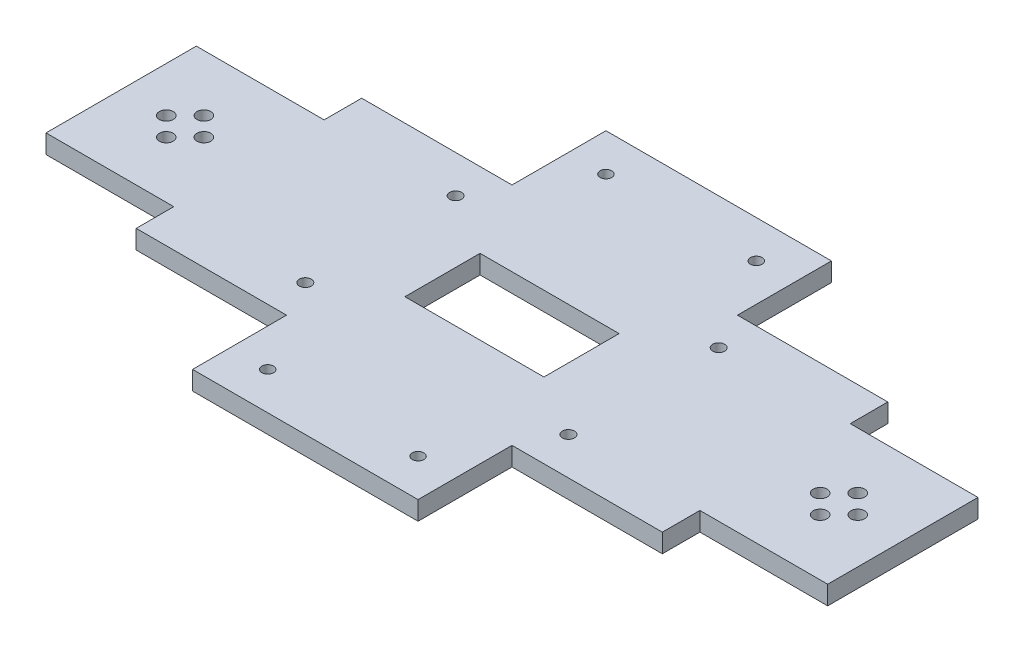
SolidWorks part; units mm, degrees
ref_plane "Front Plane" through (0, 0, 0) normal (0, 0, 1) x (1, 0, 0)
ref_plane "Top Plane" through (0, 0, 0) normal (0, 1, 0) x (1, 0, 0)
ref_plane "Right Plane" through (0, 0, 0) normal (1, 0, 0) x (0, 0, -1)
sketch "Sketch1" plane through (0, 0, 0) normal (0, 1, 0) x (1, 0, 0)
  line L0 (0, 50) -> (0, -43.3333) construction
  line L1 (104, 0) -> (87, 0) construction
  line L2 (-70, 30) -> (70, 30)
  line L3 (0, 30) -> (0, -30)
  line L4 (-70, -30) -> (70, -30)
  line L5 (70, 30) -> (70, -30)
  line L6 (70, 20) -> (104, 20)
  line L7 (70, 20) -> (70, -20)
  line L8 (70, -20) -> (104, -20)
  line L9 (104, 20) -> (104, -20)
  line L10 (104, 20) -> (70, 20) construction
  line L11 (87, 0) -> (104, 0) construction
  line L13 (104, 0) -> (87, 0) construction
  line L14 (87, 0) -> (87, 15) construction
  line L15 (-87, 0) -> (-87, 15) construction
  line L16 (-104, 0) -> (-87, 0) construction
  line L17 (-87, 0) -> (-104, 0) construction
  line L18 (-104, 20) -> (-70, 20) construction
  line L19 (-104, 0) -> (-87, 0) construction
  line L20 (-104, 20) -> (-104, -20)
  line L21 (-70, -20) -> (-104, -20)
  line L22 (-70, 20) -> (-70, -20)
  line L23 (-70, 20) -> (-104, 20)
  line L24 (-70, 30) -> (-70, -30)
  line L25 (-18.5, 10) -> (-18.5, -10)
  line L26 (-18.5, 10) -> (18.5, 10)
  line L27 (0, 10) -> (0, -10)
  line L28 (-18.5, -10) -> (18.5, -10)
  line L29 (18.5, 10) -> (18.5, -10)
  line L31 (0, 30) -> (32.0822, 30)
  line L32 (0, 30) -> (0, 55.2592)
  line L33 (0, 55.2592) -> (32.0822, 55.2592)
  line L34 (32.0822, 30) -> (32.0822, 55.2592)
  line L35 (0, -30) -> (32.0822, -30)
  line L36 (0, -30) -> (0, -49.982)
  line L37 (0, -49.982) -> (32.0822, -49.982)
  line L38 (32.0822, -30) -> (32.0822, -49.982)
  circle A0 centre (87, 5) radius 1.85
  circle A1 centre (92, 0) radius 1.85
  circle A2 centre (87, -5) radius 1.85
  circle A3 centre (82, 0) radius 1.85
  circle A4 centre (-82, 0) radius 1.85
  circle A5 centre (-87, -5) radius 1.85
  circle A6 centre (-92, 0) radius 1.85
  circle A7 centre (-87, 5) radius 1.85
  circle A8 centre (35, 20) radius 1.6
  circle A9 centre (35, -20) radius 1.6
  circle A10 centre (-35, -20) radius 1.6
  circle A11 centre (-35, 20) radius 1.6
  circle A12 centre (17.0822, -43) radius 1.55
  point P25 (87, 0)
  point P26 (70, -15)
  point P43 (-70, -15)
  point P44 (-87, 0)
  dimension "D8" = 3.7
  dimension "D9" = 5
  dimension "D11" = 5
  dimension "D12" = 5
  dimension "D13" = 17
  dimension "D14" = 10
  dimension "D7" = 35
  dimension "D17" = 20
  dimension "D18" = 3.2
  dimension "D19" = 3.2
  dimension "D20" = 40
  dimension "D21" = 3.1
  dimension "D22" = 15
  dimension "D23" = 13
  dimension "D1" = 30
  dimension "D2" = 30
  dimension "D3" = 10
  dimension "D4" = 10
  dimension "D5" = 70
  dimension "D6" = 34
  dimension "D15" = 10
  dimension "D16" = 18.5
  dimension "D10" = 4
extrude "Boss-Extrude1" add sketch "Sketch1" along normal blind 5 contours L5 L2 L3 L4 | L9 L6 L5 L8 A3 A2 A1 A0 | L22 L23 L20 L21 A6 A4 A5 A7 | L2 L24 L22 L4 L3
sketch "Sketch2" plane through (0, 5, 0) normal (0, 1, 0) x (1, 0, 0)
  line L0 (-70, 30) -> (70, 30) construction
  line L1 (-30, 30) -> (30, 30)
  line L2 (0, 30) -> (0, 55)
  line L3 (-30, 55) -> (30, 55)
  line L4 (30, 30) -> (30, 55)
  line L5 (-70, -30) -> (70, -30) construction
  line L6 (-30, -30) -> (30, -30)
  line L7 (0, -30) -> (0, -55)
  line L8 (-30, -55) -> (30, -55)
  line L9 (30, -30) -> (30, -55)
  line L10 (0, 0) -> (0, -19.3557) construction
  line L11 (-30, -30) -> (-30, -55)
  line L12 (-30, 30) -> (-30, 55)
  line L13 (0, 0) -> (30, 0) construction
  circle A0 centre (20, -45) radius 1.55
  circle A2 centre (20, 45) radius 1.55
  circle A3 centre (-20, -45) radius 1.55
  circle A4 centre (-20, 45) radius 1.55
  line M6 (-70, -30) -> (70, -30)
  line M12 (70, 30) -> (-70, 30)
  dimension "D5" = 3.1
  dimension "D6" = 10
  dimension "D7" = 10
  dimension "D1" = 25
  dimension "D2" = 25
  dimension "D3" = 30
  dimension "D4" = 30
extrude "Boss-Extrude2" add sketch "Sketch2" against normal blind 5 contours L4 L3 L2 M12 | L12 L1 L2 L3 | L11 L8 L7 A3 M6 | L9 L6 L7 L8 A0
